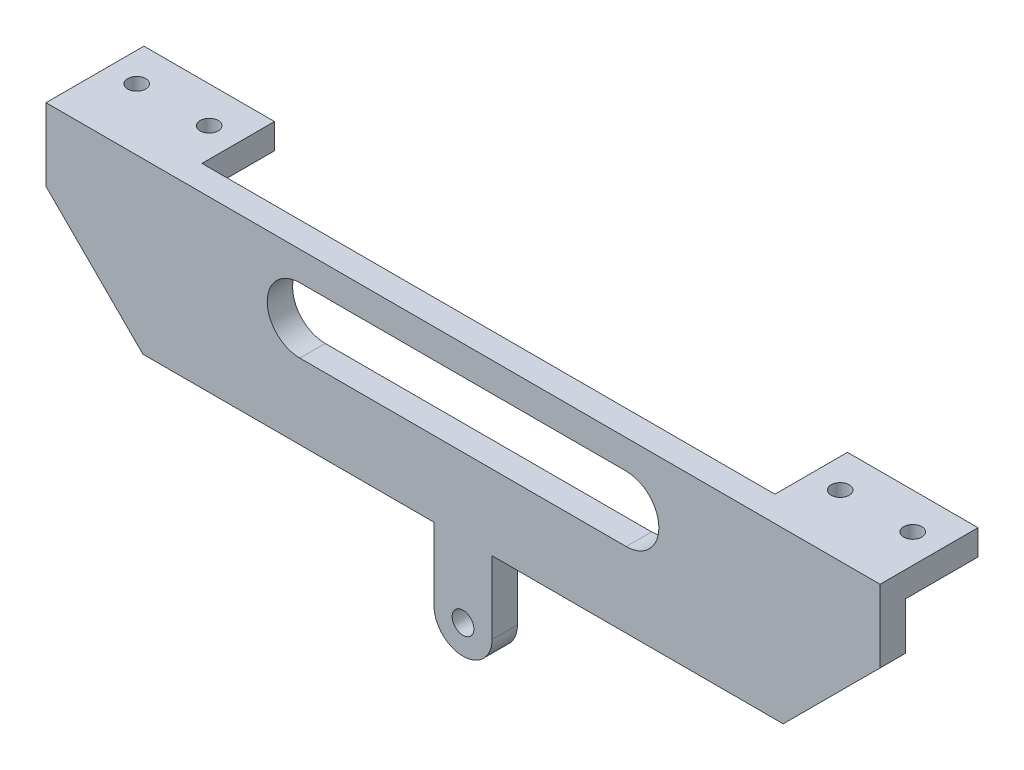
SolidWorks part; units mm, degrees
ref_plane "Front Plane" through (0, 0, 0) normal (0, 0, 1) x (1, 0, 0)
ref_plane "Top Plane" through (0, 0, 0) normal (0, 1, 0) x (1, 0, 0)
ref_plane "Right Plane" through (0, 0, 0) normal (1, 0, 0) x (0, 0, -1)
sketch "Sketch1" plane through (0, 0, 0) normal (0, 0, 1) x (1, 0, 0)
  line L0 (-100, 0) -> (100, 0) construction
  line L1 (0, 0) -> (0, 75.9094) construction
  line L2 (-40, 60) -> (40, 60) construction
  line L4 (0, 99.9354) -> (0, 75.9094) construction
  line L6 (0, 0) -> (-50, 50) construction
  line L7 (-100, 0) -> (0, 100) construction
  line L8 (0, 100) -> (100, 0) construction
  circle A0 centre (-100, 0) radius 20
  circle A1 centre (0, 0) radius 20
  circle A2 centre (100, 0) radius 20
  dimension "D4" = 40
  dimension "D1" = 200
  dimension "D2" = 100
  dimension "D3" = 80
sketch "Sketch3" plane through (0, 0, 0) normal (0, 0, 1) x (1, 0, 0)
  line L0 (-40, 60) -> (-56.5165, 43.4835) construction
  line L1 (81.9688, 8.8388) -> (95.4038, -4.5962)
  line L2 (-40, 60) -> (40, 60) construction
  line L3 (40, 60) -> (86.565, 13.435) construction
  line L4 (0, 100) -> (100, 0) construction
  line L5 (-100, 0) -> (0, 100) construction
  line L6 (44.1421, 70) -> (93.636, 20.5061)
  line L7 (-44.1421, 70) -> (44.1421, 70)
  line L8 (-44.1421, 70) -> (-63.5876, 50.5546)
  line L9 (35.8579, 50) -> (79.4939, 6.364)
  line L10 (-35.8579, 50) -> (35.8579, 50)
  line L11 (-35.8579, 50) -> (-49.4454, 36.4124)
  line L12 (-63.5876, 50.5546) -> (-49.4454, 36.4124)
  line L13 (79.4939, 6.364) -> (93.636, 20.5061)
  line L14 (104.5962, 4.5962) -> (91.1612, 18.0312)
  line L15 (0, 99.9354) -> (0, 75.9094) construction
  line L16 (-3.4532, 85.4203) -> (-6, 70)
  line L17 (3.4532, 85.4203) -> (6, 70)
  line L19 (0, 0) -> (0, 75.9094) construction
  line L20 (75.9584, 9.8995) -> (90.1005, 24.0416) construction
  circle A0 centre (100, 0) radius 10 construction
  circle A1 centre (100, 0) radius 3.5
  arc A2 (95.4038, -4.5962) -> (104.5962, 4.5962) centre (100, 0) ccw
  circle A3 centre (0, 60) radius 1.5
  circle A4 centre (0, 84.85) radius 1.5
  arc A5 (3.4532, 85.4203) -> (-3.4532, 85.4203) centre (0, 84.85) ccw
  circle A6 centre (79.4939, 13.435) radius 1
  circle A7 centre (86.565, 20.5061) radius 1
  circle A8 centre (0, 84.85) radius 3.5 construction
  circle A9 centre (100, 0) radius 6.5 construction
  circle A10 centre (-50, 50) radius 1.5
  dimension "D5" = 20
  dimension "D6" = 7
  dimension "D9" = 3
  dimension "D10" = 3
  dimension "D16" = 2
  dimension "D19" = 3
  dimension "D3" = 27.5
  dimension "D4" = 19
  dimension "D8" = 90
  dimension "D11" = 14.85
  dimension "D12" = 2
  dimension "D13" = 6
  dimension "D14" = 6
  dimension "D15" = 5
  dimension "D17" = 5
  dimension "D18" = 5
  dimension "D1" = 10
  dimension "D2" = 10
  dimension "D7" = 3
sketch "Sketch4" plane through (0, 0, 0) normal (0, 0, 1) x (1, 0, 0)
  line L0 (-86.565, 13.435) -> (-50, 50) construction
  line L1 (-100, 0) -> (0, 100) construction
  line L2 (-50, 50) -> (-13.3744, 13.3744) construction
  line L3 (0, 0) -> (-50, 50) construction
  line L4 (-79.4939, 6.364) -> (-50, 35.8579)
  line L5 (-50, 35.8579) -> (-20.4455, 6.3033)
  line L6 (-93.636, 20.5061) -> (-50, 64.1421)
  line L7 (-50, 64.1421) -> (-6.3033, 20.4455)
  line L8 (-93.636, 20.5061) -> (-79.4939, 6.364)
  line L10 (-82.1491, 9.0191) -> (-95.3424, -4.534)
  line L11 (-91.1612, 18.0312) -> (-104.5962, 4.5962)
  line L12 (-20.4455, 6.3033) -> (-6.3033, 20.4455)
  line L13 (-8.7782, 17.9706) -> (4.5962, 4.5962)
  line L14 (-17.9706, 8.7782) -> (-4.5962, -4.5962)
  line L15 (-90.1005, 24.0416) -> (-75.9584, 9.8995) construction
  line L16 (-23.981, 9.8389) -> (-9.8389, 23.981) construction
  circle A0 centre (-100, 0) radius 10 construction
  circle A1 centre (-100, 0) radius 3.5
  circle A2 centre (0, 0) radius 10 construction
  circle A3 centre (0, 0) radius 3.5
  circle A4 centre (100, 0) radius 10 construction
  arc A5 (-104.5962, 4.5962) -> (-95.3424, -4.534) centre (-100, 0) ccw
  circle A6 centre (100, 0) radius 3.5 construction
  arc A7 (-4.5962, -4.5962) -> (4.5962, 4.5962) centre (0, 0) ccw
  circle A8 centre (-100, 0) radius 20 construction
  circle A9 centre (-50, 50) radius 1.5 construction
  circle A10 centre (0, 0) radius 20 construction
  circle A11 centre (-100, 0) radius 6.5 construction
  circle A12 centre (0, 0) radius 6.5 construction
  circle A13 centre (-86.565, 20.5061) radius 1
  circle A14 centre (-79.4939, 13.435) radius 1
  circle A15 centre (-20.4455, 13.3744) radius 1
  circle A16 centre (-13.3744, 20.4455) radius 1
  circle A17 centre (-50, 50) radius 1.5
  dimension "D7" = 2
  dimension "D4" = 19
  dimension "D5" = 5
  dimension "D6" = 5
  dimension "D8" = 5
  dimension "D9" = 5
  dimension "D10" = 5
  dimension "D11" = 5
  dimension "D1" = 10
  dimension "D2" = 10
  dimension "D3" = 3
sketch "Sketch6" plane through (0, 0, 0) normal (0, 0, 1) x (1, 0, 0)
  line L0 (-57.5, 93.35) -> (57.5, 93.35)
  line L1 (57.5, 93.35) -> (57.5, 83.35)
  line L2 (57.5, 83.35) -> (44.1421, 70)
  line L3 (-57.5, 93.35) -> (-57.5, 83.35)
  line L4 (-57.5, 83.35) -> (-44.1421, 70)
  line L5 (-22.5, 84.85) -> (22.5, 84.85) construction
  line L6 (4, 60) -> (4, 70)
  line L7 (-44.1421, 70) -> (44.1421, 70) construction
  line L8 (-4, 60) -> (-4, 70)
  line L9 (-22.5, 89.35) -> (22.5, 89.35)
  line L12 (-22.5, 80.35) -> (22.5, 80.35)
  circle A0 centre (0, 60) radius 1.5 construction
  circle A1 centre (0, 60) radius 1.5
  circle A2 centre (0, 60) radius 4
  arc A5 (-22.5, 89.35) -> (-22.5, 80.35) centre (-22.5, 84.85) ccw
  arc A6 (22.5, 80.35) -> (22.5, 89.35) centre (22.5, 84.85) ccw
  point P8 (0, 93.35)
  point P23 (0, 84.85)
  dimension "D1" = 115
  dimension "D2" = 10
  dimension "D3" = 2.5
  dimension "D4" = 45
  dimension "D5" = 4
  dimension "D6" = 9
sketch "Sketch7" plane through (0, 0, 0) normal (0, 0, 1) x (1, 0, 0)
  line L0 (-4, 60) -> (-4, 70) construction
  line L1 (57.5, 83.35) -> (44.1421, 70) construction
  line L2 (22.5, 89.35) -> (-22.5, 89.35)
  line L3 (-22.5, 80.35) -> (22.5, 80.35)
  line L4 (22.5, 89.35) -> (-22.5, 89.35)
  line L5 (-22.5, 80.35) -> (22.5, 80.35)
  line L6 (57.5, 93.35) -> (57.5, 83.35) construction
  line L7 (-57.5, 93.35) -> (57.5, 93.35) construction
  line L8 (-57.5, 93.35) -> (-57.5, 83.35) construction
  line L9 (-57.5, 83.35) -> (-44.1421, 70) construction
  line L10 (4, 60) -> (4, 70) construction
  line L11 (-4, 60) -> (-4, 70)
  line L12 (57.5, 83.35) -> (44.1421, 70)
  line L13 (57.5, 93.35) -> (57.5, 83.35)
  line L14 (-57.5, 93.35) -> (57.5, 93.35)
  line L15 (-57.5, 93.35) -> (-57.5, 83.35)
  line L16 (-57.5, 83.35) -> (-44.1421, 70)
  line L17 (4, 60) -> (4, 70)
  line L18 (-44.1421, 70) -> (44.1421, 70) construction
  line L19 (-44.1421, 70) -> (-4, 70)
  line L20 (4, 70) -> (44.1421, 70)
  circle A1 centre (0, 60) radius 4
  arc A2 (-4, 60) -> (4, 60) centre (0, 60) ccw
  circle A3 centre (0, 60) radius 1.5
  circle A4 centre (0, 60) radius 1.5
  arc A6 (22.5, 80.35) -> (22.5, 89.35) centre (22.5, 84.85) ccw
  arc A7 (-22.5, 89.35) -> (-22.5, 80.35) centre (-22.5, 84.85) ccw
  arc A8 (22.5, 80.35) -> (22.5, 89.35) centre (22.5, 84.85) ccw
  arc A9 (-22.5, 89.35) -> (-22.5, 80.35) centre (-22.5, 84.85) ccw
  point P4 (-37.5043, 93.35)
  point P19 (-74.2584, 93.35)
  dimension "D1" = 0
  dimension "D2" = 0
  dimension "D3" = 0
extrude "Boss-Extrude1" add sketch "Sketch7" along normal blind 3.5
sketch "Sketch10" plane through (0, 93.35, 0) normal (0, 1, 0) x (1, 0, 0)
  line L0 (-57.5, 0) -> (-57.5, 10)
  line L1 (-57.5, 10) -> (-39.5, 10)
  line L2 (-39.5, 10) -> (-39.5, 0)
  line L3 (57.5, 0) -> (-57.5, 0) construction
  line L4 (-57.5, 5) -> (-39.5, 5) construction
  line L5 (-48.5, 10) -> (-48.5, 5) construction
  line L6 (0, 0) -> (0, 46.6981) construction
  line L7 (48.5, 10) -> (48.5, 5) construction
  line L8 (57.5, 5) -> (39.5, 5) construction
  line L9 (39.5, 10) -> (39.5, 0)
  line L10 (57.5, 10) -> (39.5, 10)
  line L11 (57.5, 0) -> (57.5, 10)
  circle A0 centre (-53.5, 5) radius 1.25
  circle A1 centre (-43.5, 5) radius 1.25
  circle A2 centre (43.5, 5) radius 1.25
  circle A3 centre (53.5, 5) radius 1.25
  line M6 (57.5, 0) -> (-57.5, 0)
  dimension "D3" = 2.5
  dimension "D1" = 10
  dimension "D2" = 18
  dimension "D4" = 10
  dimension "D5" = 5
extrude "Boss-Extrude3" add sketch "Sketch10" against normal blind 3.5 contours L2 L1 L0 A1 A0 M6 | L11 L10 L9 A2 A3 M6
